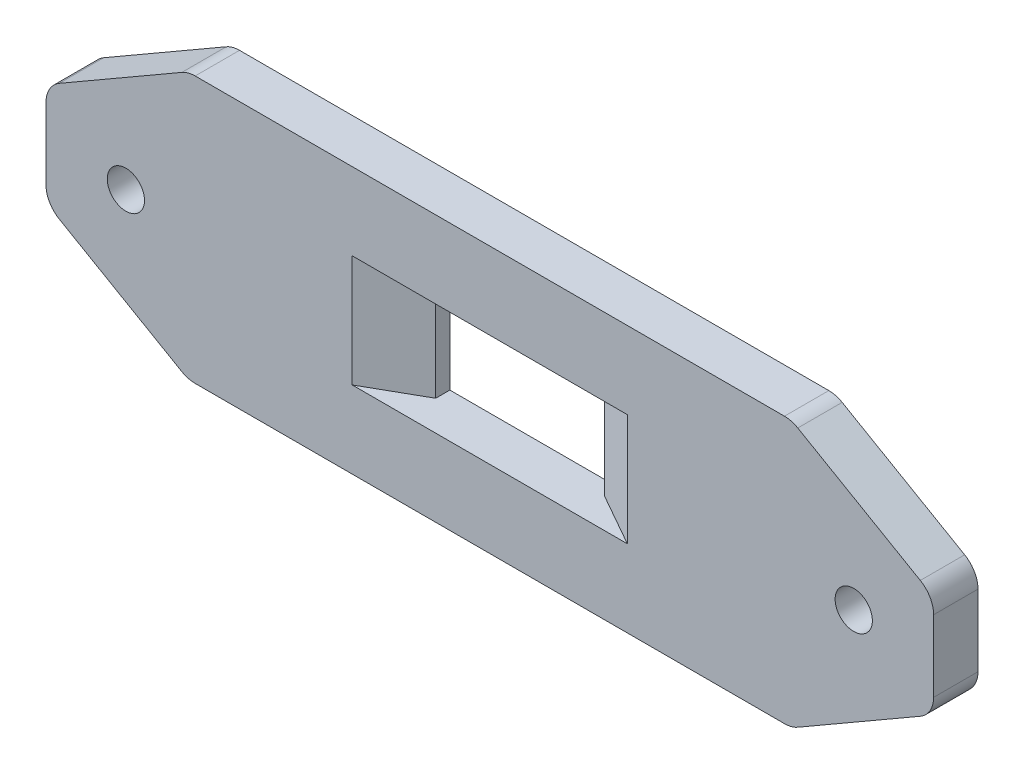
SolidWorks part; units mm, degrees
ref_plane "Front Plane" through (0, 0, 0) normal (0, 0, 1) x (1, 0, 0)
ref_plane "Top Plane" through (0, 0, 0) normal (0, 1, 0) x (1, 0, 0)
ref_plane "Right Plane" through (0, 0, 0) normal (1, 0, 0) x (0, 0, -1)
sketch "Sketch1" plane through (0, 0, 0) normal (0, 0, 1) x (1, 0, 0)
  line L1 (0, 0) -> (-100, 0)
  line L2 (0, 0) -> (0, 30)
  line L3 (0, 30) -> (-100, 30)
  line L4 (-100, 0) -> (-100, 30)
  dimension "D1" = 30
  dimension "D2" = 100
extrude "Boss-Extrude1" add sketch "Sketch1" along normal blind 5
chamfer "Chamfer1" distance 16 angle 30 4 edges at (0, 30, 2.5) (0, 0, 2.5) (-100, 0, 2.5) (-100, 30, 2.5)
fillet "Fillet1" radius 3 8 edges at (-100, 20.7624, 2.5) (-100, 9.2376, 2.5) (-84, 0, 2.5) (-84, 30, 2.5) (-16, 30, 2.5) (0, 20.7624, 2.5) (0, 9.2376, 2.5) (-16, 0, 2.5)
sketch "Sketch2" plane through (0, 0, 5) normal (0, 0, 1) x (1, 0, 0)
  line L0 (-16.8038, 30) -> (-83.1962, 30) construction
  line L1 (-100, 19.0303) -> (-100, 10.9697) construction
  circle A0 centre (-91, 15) radius 2.1
  circle A1 centre (-9, 15) radius 2.1
  dimension "D1" = 4.2
  dimension "D2" = 4.2
  dimension "D3" = 82
  dimension "D4" = 15
  dimension "D5" = 15
  dimension "D6" = 9
extrude "Cut-Extrude1" cut sketch "Sketch2" against normal through all
sketch "Sketch3" plane through (0, 0, 5) normal (0, 0, 1) x (1, 0, 0)
  line L0 (-83.1962, 0) -> (-16.8038, 0) construction
  line L1 (-59.5, 8.7) -> (-40.5, 8.7)
  line L2 (-59.5, 8.7) -> (-59.5, 21.3)
  line L3 (-59.5, 21.3) -> (-40.5, 21.3)
  line L4 (-40.5, 8.7) -> (-40.5, 21.3)
  line L5 (-100, 19.0303) -> (-100, 10.9697) construction
  dimension "D1" = 12.6
  dimension "D2" = 19
  dimension "D3" = 8.7
  dimension "D4" = 40.5
extrude "Cut-Extrude2" cut sketch "Sketch3" against normal through all
chamfer "Chamfer2" distance 6 distance2 3.4 2 edges at (-40.5, 15, 5) (-59.5, 15, 5)
